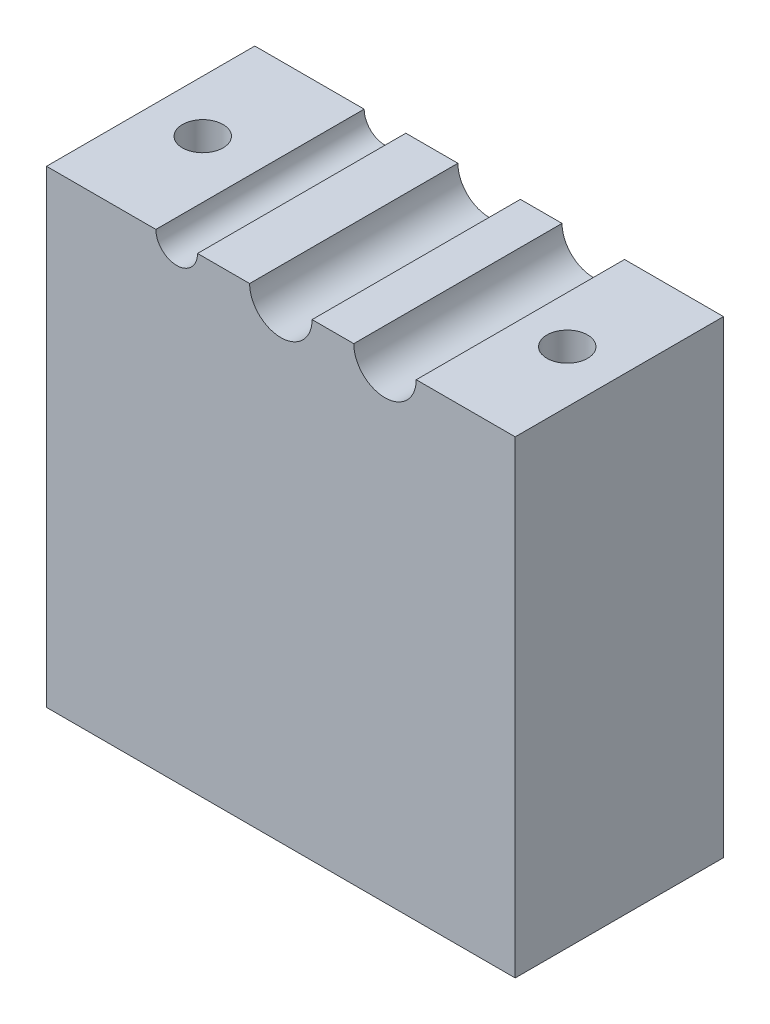
SolidWorks part; units mm, degrees
ref_plane "Front Plane" through (0, 0, 0) normal (0, 0, 1) x (1, 0, 0)
ref_plane "Top Plane" through (0, 0, 0) normal (0, 1, 0) x (1, 0, 0)
ref_plane "Right Plane" through (0, 0, 0) normal (1, 0, 0) x (0, 0, -1)
sketch "Sketch1" plane through (0, 0, 0) normal (0, 0, 1) x (1, 0, 0)
  line L0 (0, 0) -> (0, 22.5) construction
  line L1 (-22.5, -22.5) -> (22.5, -22.5)
  line L2 (-22.5, -22.5) -> (-22.5, 22.5)
  line L3 (-22.5, 22.5) -> (22.5, 22.5) construction
  line L4 (22.5, -22.5) -> (22.5, 22.5)
  line L5 (-22.5, -22.5) -> (22.5, 22.5) construction
  line L6 (-22.5, 22.5) -> (22.5, -22.5) construction
  line L7 (-22.5, 22.5) -> (-12, 22.5)
  line L8 (-8, 22.5) -> (-3, 22.5)
  line L9 (3, 22.5) -> (7, 22.5)
  line L10 (13, 22.5) -> (22.5, 22.5)
  circle A0 centre (-10, 22.5) radius 2 construction
  circle A1 centre (0, 22.5) radius 3 construction
  circle A2 centre (10, 22.5) radius 3 construction
  arc A3 (-12, 22.5) -> (-8, 22.5) centre (-10, 22.5) ccw
  arc A4 (-3, 22.5) -> (3, 22.5) centre (0, 22.5) ccw
  arc A5 (7, 22.5) -> (13, 22.5) centre (10, 22.5) ccw
  point P0 (0, 0)
  dimension "D3" = 4
  dimension "D4" = 6
  dimension "D5" = 6
  dimension "D1" = 45
  dimension "D2" = 45
  dimension "D6" = 10
  dimension "D7" = 10
extrude "Boss-Extrude1" add sketch "Sketch1" along normal blind 20
sketch "Sketch2" plane through (0, 22.5, 0) normal (0, 1, 0) x (1, 0, 0)
  line L0 (-22.5, -10) -> (22.5, -10) construction
  line L1 (-22.5, -20) -> (-22.5, 0) construction
  line L2 (22.5, -20) -> (22.5, 0) construction
  line L3 (0, 0) -> (0, -20) construction
  line L4 (-3, -20) -> (3, -20) construction
  circle A0 centre (-17.5, -10) radius 1.95
  circle A1 centre (17.5, -10) radius 1.95
  dimension "D1" = 3.9
  dimension "D2" = 5
extrude "Cut-Extrude1" cut sketch "Sketch2" against normal blind 20
